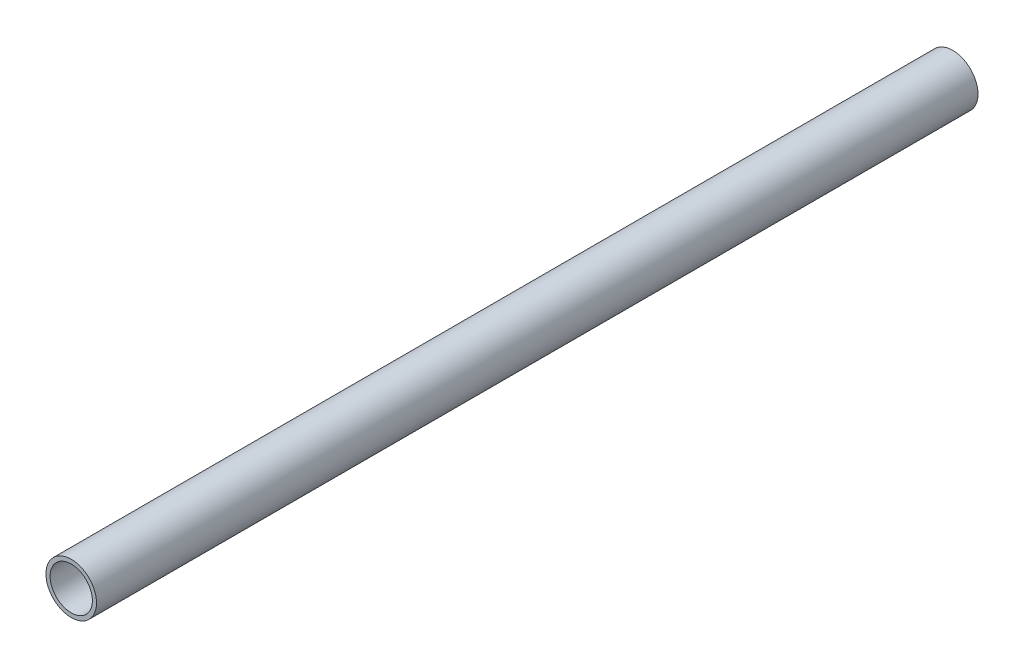
SolidWorks part; units mm, degrees
ref_plane "Front Plane" through (0, 0, 0) normal (0, 0, 1) x (1, 0, 0)
ref_plane "Top Plane" through (0, 0, 0) normal (0, 1, 0) x (1, 0, 0)
ref_plane "Right Plane" through (0, 0, 0) normal (1, 0, 0) x (0, 0, -1)
sketch "Sketch1" plane through (0, 0, 0) normal (0, 0, 1) x (1, 0, 0)
  circle A0 centre (0, 0) radius 24.13
  circle A1 centre (0, 0) radius 20.193
  dimension "D1" = 48.26
  dimension "D2" = 40.386
extrude "Boss-Extrude1" add sketch "Sketch1" along normal blind 841.375
